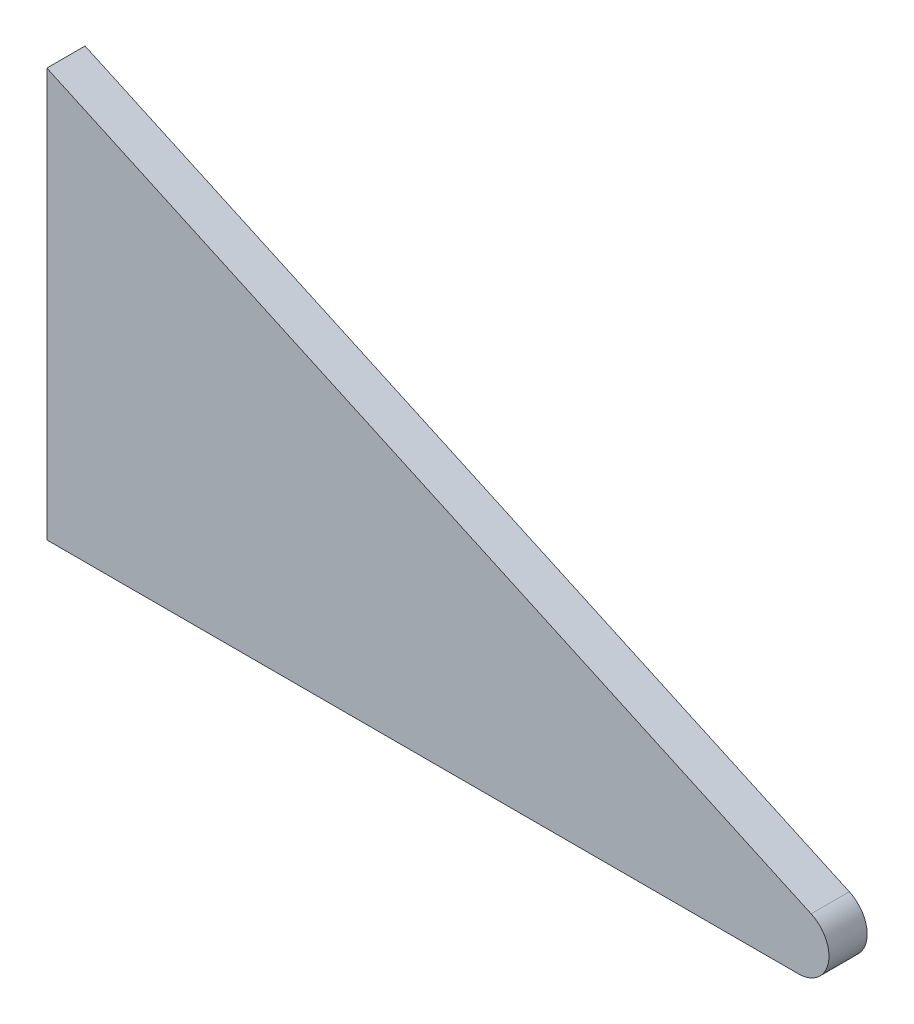
SolidWorks part; units mm, degrees
ref_plane "Front Plane" through (0, 0, 0) normal (0, 0, 1) x (1, 0, 0)
ref_plane "Top Plane" through (0, 0, 0) normal (0, 1, 0) x (1, 0, 0)
ref_plane "Right Plane" through (0, 0, 0) normal (1, 0, 0) x (0, 0, -1)
sketch "Sketch1" plane through (0, 0, 0) normal (0, 0, 1) x (1, 0, 0)
  line L1 (90.184, 0) -> (152.6257, 0)
  line L2 (153.684, 4.849) -> (90.184, 33.9542)
  line L3 (120.8757, 7.62) -> (76.3516, 7.62) construction
  line L4 (90.184, 0) -> (90.184, 33.9542)
  arc A2 (152.6257, 0) -> (153.684, 4.849) centre (152.6257, 2.54) ccw
  point P12 (164.2633, 0)
  dimension "D2" = 11.6376
  dimension "D7" = 7.62
  dimension "D10" = 63.5
extrude "Extrude1" add sketch "Sketch1" along normal blind 3.175
